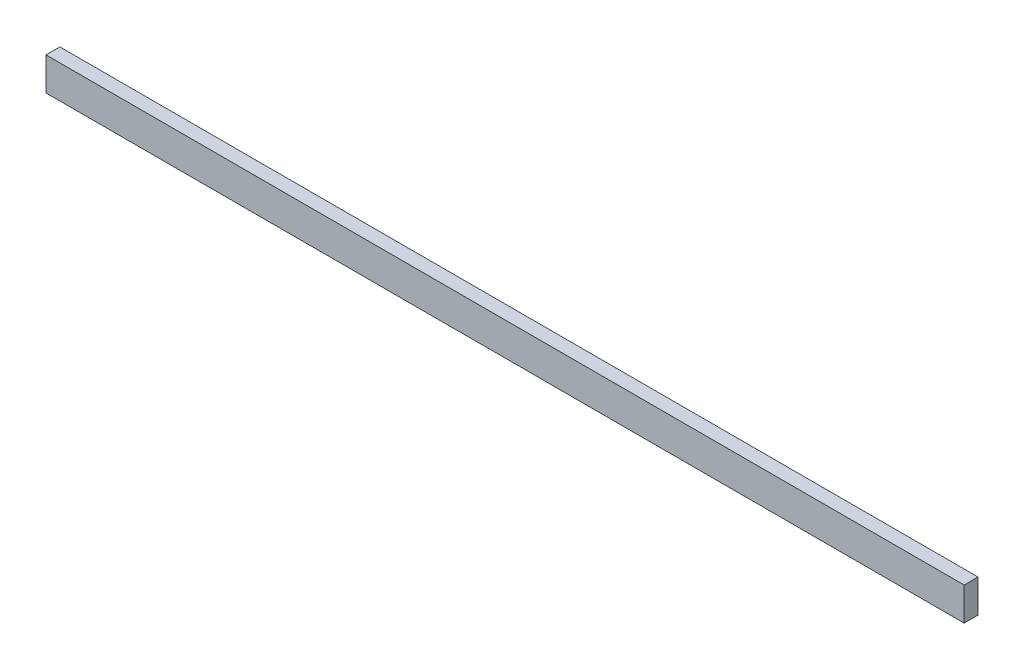
SolidWorks part; units mm, degrees
ref_plane "Front Plane" through (0, 0, 0) normal (0, 0, 1) x (1, 0, 0)
ref_plane "Top Plane" through (0, 0, 0) normal (0, 1, 0) x (1, 0, 0)
ref_plane "Right Plane" through (0, 0, 0) normal (1, 0, 0) x (0, 0, -1)
sketch "Sketch1" plane through (0, 0, 0) normal (0, 0, 1) x (1, 0, 0)
  line L1 (0, 0) -> (219.075, 0)
  line L2 (0, 0) -> (0, 7.874)
  line L3 (0, 7.874) -> (219.075, 7.874)
  line L4 (219.075, 0) -> (219.075, 7.874)
  dimension "D1" = 219.075
  dimension "D2" = 7.874
extrude "Boss-Extrude1" add sketch "Sketch1" along normal blind 3.302
equation "\"depth\"= 7.3"
equation "\"height\"= 9.5"
equation "\"width\"= 8.50"
equation "\"flipWidth\"= 6.5"
equation "\"flipHeight\"= 4"
equation "\"spindleLength\"= 7.75"
equation "\"bearingID\"= 0.1559"
equation "\"bearingOD\"= 0.3539\t"
equation "\"motorWidth\"= 0.79"
equation "\"motorHeight\"= 1.0"
equation "\"motorLength\"= 1.58"
equation "\"spindleMaxDiam\"= 2.75"
equation "\"totalLength\"= 15"
equation "\"stopperWidth\"= 0.13"
equation "\"stopperHeight\"= 0.31"
equation "\"stopperLength\"= \"width\" + 1/8"
equation "\"D1@Sketch1\"=\"stopperLength\""
equation "\"D2@Sketch1\"=\"stopperHeight\""
equation "\"D1@Boss-Extrude1\"=\"stopperWidth\""
